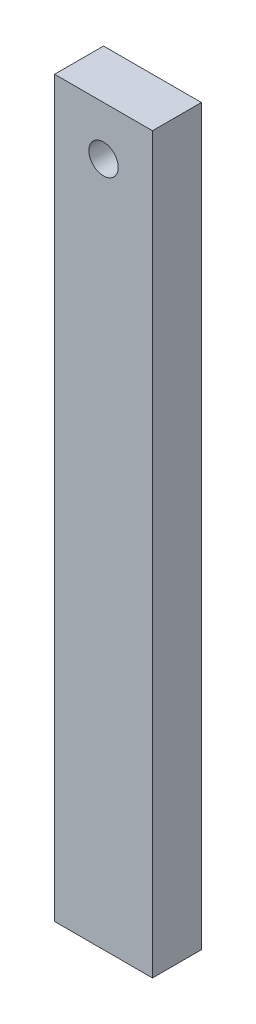
SolidWorks part; units mm, degrees
ref_plane "Front Plane" through (0, 0, 0) normal (0, 0, 1) x (1, 0, 0)
ref_plane "Top Plane" through (0, 0, 0) normal (0, 1, 0) x (1, 0, 0)
ref_plane "Right Plane" through (0, 0, 0) normal (1, 0, 0) x (0, 0, -1)
sketch "Sketch2" plane through (0, 0, 0) normal (0, 0, 1) x (1, 0, 0)
  line L1 (-10, -75) -> (10, -75)
  line L2 (-10, -75) -> (-10, 75)
  line L3 (-10, 75) -> (10, 75)
  line L4 (10, -75) -> (10, 75)
  line L5 (-10, -75) -> (10, 75) construction
  line L6 (-10, 75) -> (10, -75) construction
  point P0 (0, 0)
  dimension "D1" = 150
  dimension "D2" = 20
extrude "Boss-Extrude1" add sketch "Sketch2" along normal blind 10
sketch "Sketch3" plane through (0, 0, 10) normal (0, 0, 1) x (1, 0, 0)
  line L0 (10, -75) -> (10, 75) construction
  circle A0 centre (0, 65) radius 3
  dimension "D3" = 6
  dimension "D1" = 65
  dimension "D2" = 10
extrude "Cut-Extrude1" cut sketch "Sketch3" against normal up to surface (10 mm away) up to face at (0, 0, 0)
